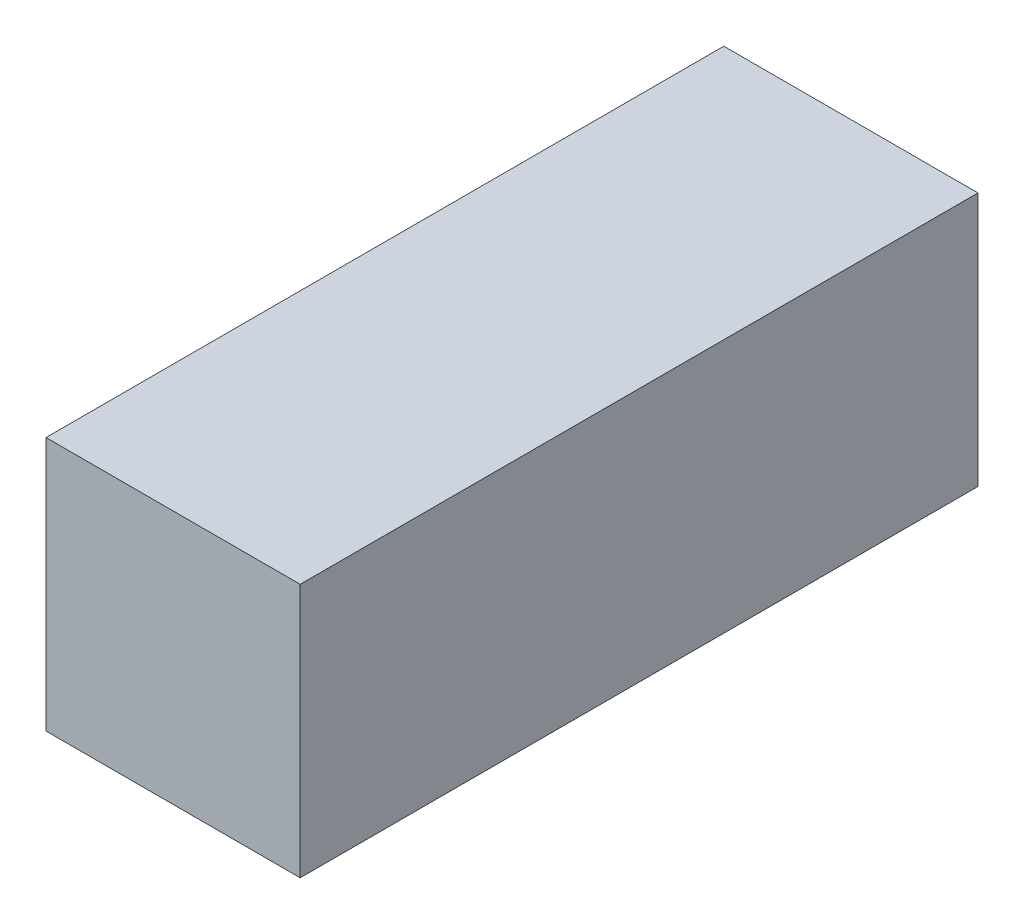
SolidWorks part; units mm, degrees
ref_plane "Front Plane" through (0, 0, 0) normal (0, 0, 1) x (1, 0, 0)
ref_plane "Top Plane" through (0, 0, 0) normal (0, 1, 0) x (1, 0, 0)
ref_plane "Right Plane" through (0, 0, 0) normal (1, 0, 0) x (0, 0, -1)
sketch "Sketch1" plane through (0, 0, 0) normal (0, 0, 1) x (1, 0, 0)
  line L1 (-7.5, -7.5) -> (7.5, -7.5)
  line L2 (-7.5, -7.5) -> (-7.5, 7.5)
  line L3 (-7.5, 7.5) -> (7.5, 7.5)
  line L4 (7.5, -7.5) -> (7.5, 7.5)
  line L5 (-7.5, -7.5) -> (7.5, 7.5) construction
  line L6 (-7.5, 7.5) -> (7.5, -7.5) construction
  point P0 (0, 0)
  dimension "D1" = 15
extrude "Boss-Extrude1" add sketch "Sketch1" along normal mid plane 40
sketch "Sketch2" plane through (0, 0, 0) normal (0, 0, 1) x (1, 0, 0)
  circle A0 centre (0, 0) radius 5
  dimension "D1" = 10
extrude "Cut-Extrude1" cut sketch "Sketch2" against normal mid plane 35
